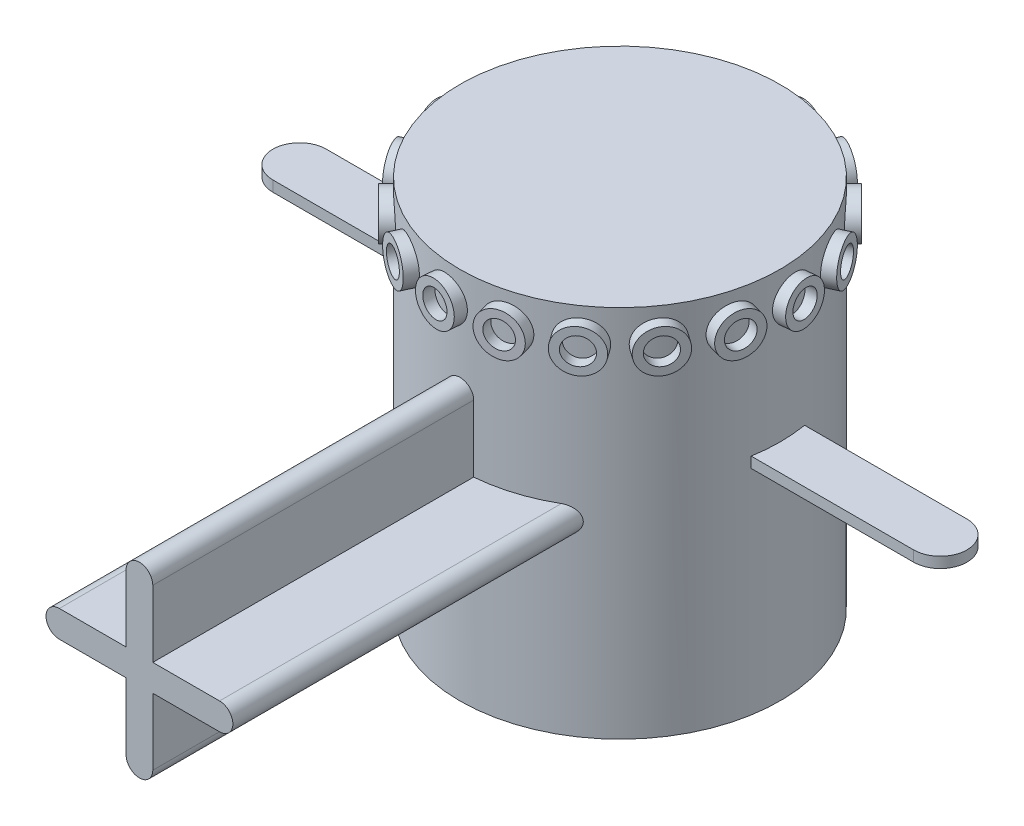
SolidWorks part; units mm, degrees
ref_plane "Front Plane" through (0, 0, 0) normal (0, 0, 1) x (1, 0, 0)
ref_plane "Top Plane" through (0, 0, 0) normal (0, 1, 0) x (1, 0, 0)
ref_plane "Right Plane" through (0, 0, 0) normal (1, 0, 0) x (0, 0, -1)
sketch "Sketch2" plane through (0, 0, 0) normal (0, 1, 0) x (1, 0, 0)
  circle A0 centre (0, 0) radius 38.1
  dimension "D1" = 76.2
extrude "Boss-Extrude1" add sketch "Sketch2" along normal blind 88.9
ref_plane "Plane1" through (0, 50.8, 0) normal (0, 1, 0) x (1, 0, 0)
sketch "Sketch3" plane through (0, 50.8, 0) normal (0, 1, 0) x (1, 0, 0)
  line L0 (-76.2, 0) -> (76.2, 0) construction
  line L2 (-76.2, 6.35) -> (76.2, 6.35)
  line L3 (-76.2, -6.35) -> (76.2, -6.35)
  arc A0 (-76.2, 6.35) -> (-76.2, -6.35) centre (-76.2, 0) ccw
  arc A1 (76.2, -6.35) -> (76.2, 6.35) centre (76.2, 0) ccw
  point P5 (0, 0)
  dimension "D2" = 12.7
  dimension "D1" = 152.4
extrude "Boss-Extrude2" add sketch "Sketch3" along normal blind 2.54
ref_plane "Plane2" through (0, 0, 38.1) normal (0, 0, 1) x (1, 0, 0)
sketch "Sketch4" plane through (0, 0, 38.1) normal (0, 0, 1) x (1, 0, 0)
  line L0 (0, 88.9) -> (0, 0) construction
  line L1 (38.1, 88.9) -> (-38.1, 88.9) construction
  line L2 (-38.1, 44.45) -> (38.1, 44.45) construction
  line L3 (-38.1, 50.8) -> (-38.1, 0) construction
  line L4 (38.1, 0) -> (38.1, 50.8) construction
  line L5 (-19.05, 44.45) -> (19.05, 44.45) construction
  line L6 (-19.05, 47.625) -> (19.05, 47.625)
  line L7 (-19.05, 41.275) -> (19.05, 41.275)
  line L8 (0, 63.5) -> (0, 25.4) construction
  line L9 (3.175, 63.5) -> (3.175, 25.4)
  line L10 (-3.175, 63.5) -> (-3.175, 25.4)
  arc A0 (-19.05, 47.625) -> (-19.05, 41.275) centre (-19.05, 44.45) ccw
  arc A1 (19.05, 41.275) -> (19.05, 47.625) centre (19.05, 44.45) ccw
  arc A2 (3.175, 63.5) -> (-3.175, 63.5) centre (0, 63.5) ccw
  arc A3 (-3.175, 25.4) -> (3.175, 25.4) centre (0, 25.4) ccw
  point P13 (0, 44.45)
  point P19 (0, 44.45)
  dimension "D2" = 6.35
  dimension "D1" = 38.1
  dimension "D3" = 38.1
  dimension "D4" = 6.35
extrude "Boss-Extrude3" add sketch "Sketch4" along normal blind 76.2 and the other way up to surface contours L9 A2 L10 L6 | L7 A1 L6 L9 | L6 A0 L7 L10 | L10 A3 L9 L7 | L6 L10 L7 L9
sketch "Sketch5" plane through (0, 88.9, 0) normal (0, 1, 0) x (1, 0, 0)
  line L0 (-45.9054, 0) -> (45.9054, 0) construction
  line L1 (0, 0) -> (26.9408, 26.9408) construction
  circle A0 centre (0, 0) radius 38.1 construction
  point P4 (0, 0)
  dimension "D1" = 45
ref_plane "Plane3" through (26.9408, 88.9, -26.9408) normal (0.7071, 0, -0.7071) x (-0.7071, 0, -0.7071)
sketch "Sketch6" plane through (26.9408, 88.9, -26.9408) normal (0.7071, 0, -0.7071) x (-0.7071, 0, -0.7071)
  line L0 (32.46, 0) -> (-32.46, 0) construction
  circle A0 centre (0, -7.62) radius 3.175
  circle A1 centre (0, -7.62) radius 5.08
  point P5 (0, 0)
  dimension "D1" = 6.35
  dimension "D3" = 10.16
  dimension "D2" = 7.62
extrude "Boss-Extrude4" add sketch "Sketch6" along normal blind 2.54 and the other way up to surface contours A1 A0
pattern_circular "CirPattern1" count 18 over 360 about axis through (0, 0, 0) along (0, 1, 0) of "Boss-Extrude4"
